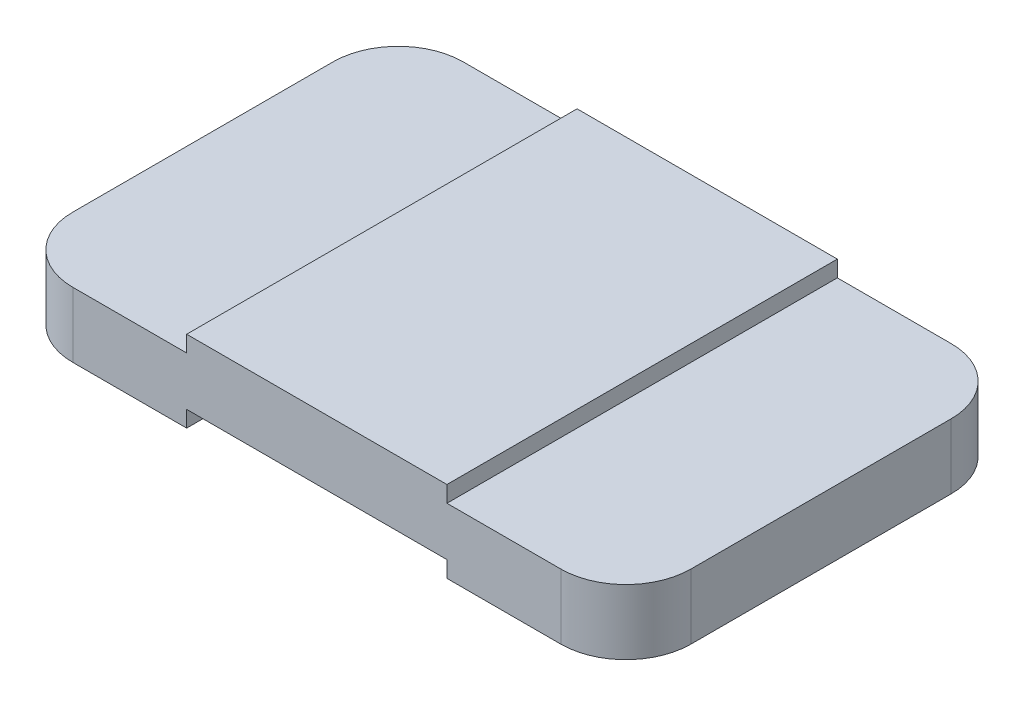
SolidWorks part; units mm, degrees
ref_plane "Front Plane" through (0, 0, 0) normal (0, 0, 1) x (1, 0, 0)
ref_plane "Top Plane" through (0, 0, 0) normal (0, 1, 0) x (1, 0, 0)
ref_plane "Right Plane" through (0, 0, 0) normal (1, 0, 0) x (0, 0, -1)
sketch "Sketch1" plane through (0, 0, 0) normal (0, 0, 1) x (1, 0, 0)
  line L0 (0, 0) -> (1.375, 0)
  line L1 (1.375, 0) -> (1.375, 0.125)
  line L2 (1.375, 0.125) -> (3.375, 0.125)
  line L3 (3.375, 0.125) -> (3.375, 0)
  line L4 (3.375, 0) -> (4.75, 0)
  line L5 (4.75, 0) -> (4.75, 0.5)
  line L6 (4.75, 0.5) -> (3.375, 0.5)
  line L7 (3.375, 0.5) -> (3.375, 0.625)
  line L8 (3.375, 0.625) -> (1.375, 0.625)
  line L9 (1.375, 0.625) -> (1.375, 0.5)
  line L10 (1.375, 0.5) -> (0, 0.5)
  line L11 (0, 0.5) -> (0, 0)
  point P11 (0, 0)
  dimension "D1" = 0.125
  dimension "D2" = 0.125
  dimension "D3" = 0.625
  dimension "D4" = 4.75
  dimension "D5" = 1.375
  dimension "D6" = 1.375
  dimension "D7" = 1.375
  dimension "D8" = 1.375
extrude "Boss-Extrude1" add sketch "Sketch1" against normal blind 3
sketch "Sketch2" plane through (0, 0.5, 0) normal (0, 1, 0) x (1, 0, 0)
  line L0 (1.375, 3) -> (0, 3) construction
  line L1 (4.75, 3) -> (3.375, 3) construction
  point P0 (0.281, 2.5)
  point P1 (2.105, 2.5)
  point P2 (2.105, 0.5)
  point P3 (0.281, 0.5)
  dimension "D1" = 2
  dimension "D2" = 0.5
  dimension "D3" = 0.5
  dimension "D4" = 2
fillet "Fillet1" radius 0.5 4 edges at (4.75, 0.25, -3) (4.75, 0.25, 0) (0, 0.25, -3) (0, 0.25, 0)
